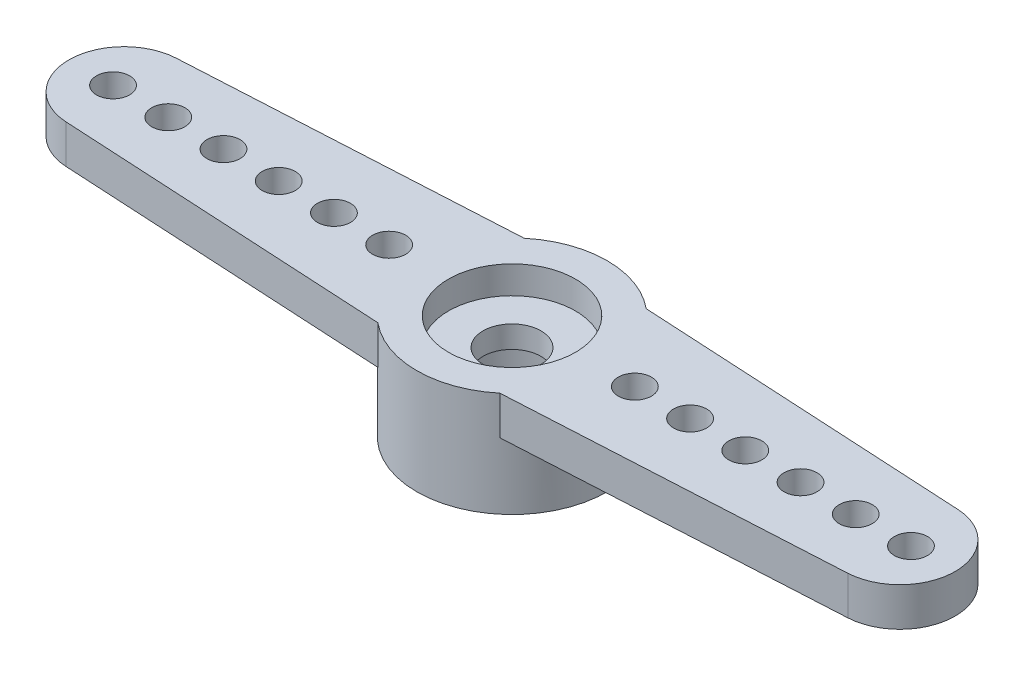
SolidWorks part; units mm, degrees
material "PVC Rígido"
ref_plane "Plano frontal" through (0, 0, 0) normal (0, 0, 1) x (1, 0, 0)
ref_plane "Plano superior" through (0, 0, 0) normal (0, 1, 0) x (1, 0, 0)
ref_plane "Plano direito" through (0, 0, 0) normal (1, 0, 0) x (0, 0, -1)
sketch "Esboço1" plane through (0, 0, 0) normal (0, 1, 0) x (1, 0, 0)
  line L0 (0, 0) -> (-14.05, 0) construction
  line L1 (-14.1591, 1.997) -> (-2.2091, 2.65)
  line L2 (-2.2091, -2.65) -> (-14.1591, -1.997)
  arc A0 (-2.2091, -2.65) -> (-2.2091, 2.65) centre (0, 0) ccw
  arc A1 (-14.1591, 1.997) -> (-14.1591, -1.997) centre (-14.05, 0) ccw
  dimension "D1" = 6.9
  dimension "D2" = 4
  dimension "D3" = 19.5
  dimension "D4" = 5.3
extrude "Ressalto-extrusão1" add sketch "Esboço1" against normal blind 1.4
sketch "Esboço2" plane through (0, -1.4, 0) normal (0, -1, 0) x (1, 0, 0)
  arc A0 (-2.2091, -2.65) -> (-2.2091, 2.65) centre (0, 0) ccw construction
  circle A1 centre (0, 0) radius 3.45
extrude "Ressalto-extrusão2" add sketch "Esboço2" along normal offset from surface (2.4 mm away) 3.8 up to face at (-7.242, 0, 0)
hole_wizard "Furo4" positions "Esboço9" profile "Esboço10" legacy end condition through all
sketch "Esboço9" plane through (0, 0, 0) normal (0, 1, 0) x (1, 0, 0)
  line L1 (-14.45, 0) -> (0, 0) construction
  arc A2 (-14.1591, 1.997) -> (-14.1591, -1.997) centre (-14.05, 0) ccw construction
  point P0 (-14.45, 0)
  point P19 (-16.05, 0)
  dimension "D1" = 1.6
sketch "Esboço10" plane through (-14.45, 0, 0) normal (1, 0, 0) x (0, 0, 1)
  line L0 (0, 0) -> (0, 3.8)
  line L1 (0, 3.8) -> (0.6, 3.8)
  line L2 (0.6, 3.8) -> (0.6, 0)
  line L3 (0.6, 0) -> (0, 0)
  line L4 (0, 110) -> (0, -10) construction
  dimension "Diameter" = 1.2
  dimension "Depth" = 3.8
pattern_linear "Padrão linear1" count 6 spacing 2 along (1, 0, 0) of "Furo4"
pattern_circular "PadrãoCircular2" count 2 over 360 about axis through (0, 0, 0) along (0, 1, 0) of "Ressalto-extrusão1", "Furo4", "Padrão linear1"
hole_wizard "Furo1" positions "Esboço3" profile "Esboço4" legacy
sketch "Esboço3" plane through (0, -3.8, 0) normal (0, -1, 0) x (-1, 0, 0)
  point P0 (0, 0)
sketch "Esboço4" plane through (0, -3.8, 0) normal (1, 0, 0) x (0, 0, -1)
  line L0 (0, 0) -> (0, 2)
  line L1 (0, 2) -> (2.475, 2)
  line L2 (2.475, 2) -> (2.475, 0)
  line L3 (2.475, 0) -> (0, 0)
  line L4 (0, 110) -> (0, -10) construction
  dimension "Diameter" = 4.95
  dimension "Depth" = 2
hole_wizard "Furo2" positions "Esboço5" profile "Esboço6" legacy
sketch "Esboço5" plane through (0, 0, 0) normal (0, 1, 0) x (1, 0, 0)
  point P0 (0, 0)
sketch "Esboço6" plane through (0, 0, 0) normal (1, 0, 0) x (0, 0, 1)
  line L0 (0, 0) -> (0, 1)
  line L1 (0, 1) -> (2.3, 1)
  line L2 (2.3, 1) -> (2.3, 0)
  line L3 (2.3, 0) -> (0, 0)
  line L4 (0, 110) -> (0, -10) construction
  dimension "Diameter" = 4.6
  dimension "Depth" = 1
hole_wizard "Furo3" positions "Esboço7" profile "Esboço8" legacy end condition through all
sketch "Esboço7" plane through (0, 0, 0) normal (0, 1, 0) x (1, 0, 0)
  point P0 (0, 0)
sketch "Esboço8" plane through (0, 0, 0) normal (1, 0, 0) x (0, 0, 1)
  line L0 (0, 0) -> (0, 3.8)
  line L1 (0, 3.8) -> (1.05, 3.8)
  line L2 (1.05, 3.8) -> (1.05, 0)
  line L3 (1.05, 0) -> (0, 0)
  line L4 (0, 110) -> (0, -10) construction
  dimension "Diameter" = 2.1
  dimension "Depth" = 3.8
sketch "Esboço11" plane through (0, -3.8, 0) normal (0, -1, 0) x (1, 0, 0)
  line L0 (-0.0981, 2.4731) -> (0, 2.375)
  line L1 (0, 2.375) -> (0.0981, 2.4731)
  line L2 (0, 0) -> (0, 2.475) construction
  circle A0 centre (0, 0) radius 2.375 construction
  circle A1 centre (0, 0) radius 2.475
  arc A2 (0.0981, 2.4731) -> (-0.0981, 2.4731) centre (0, 0) ccw
  dimension "D3" = 4.75
  dimension "D2" = 0.1
  dimension "D1" = 0
extrude "Ressalto-extrusão3" add sketch "Esboço11" against normal up to surface (2 mm away) up to face at (0, -1.8, 1.05)
